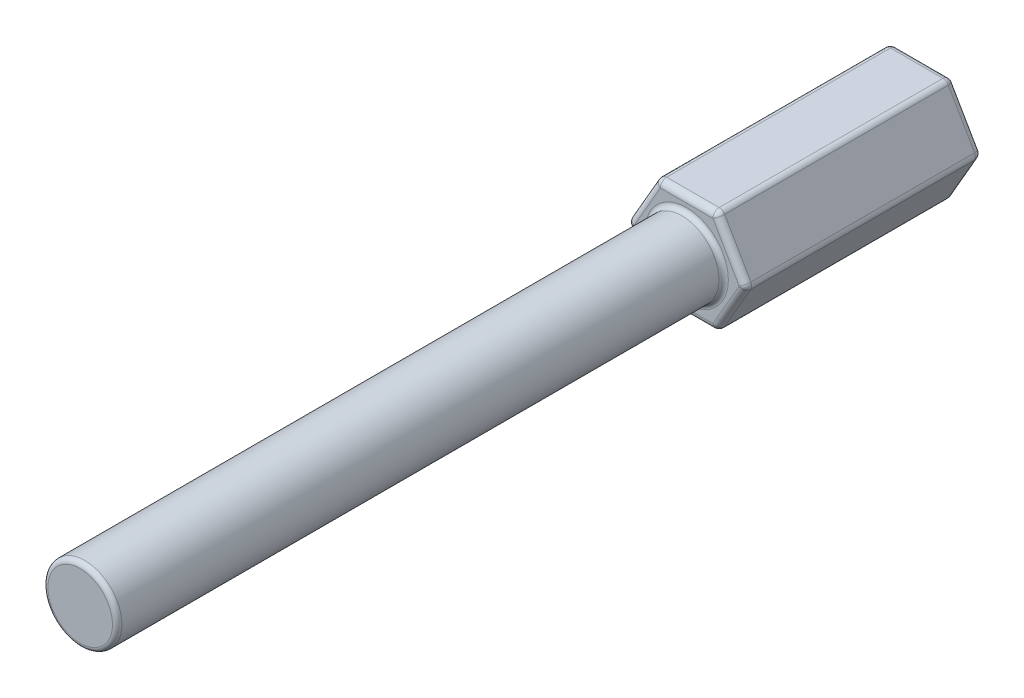
SolidWorks part; units mm, degrees
ref_plane "Front Plane" through (0, 0, 0) normal (0, 0, 1) x (1, 0, 0)
ref_plane "Top Plane" through (0, 0, 0) normal (0, 1, 0) x (1, 0, 0)
ref_plane "Right Plane" through (0, 0, 0) normal (1, 0, 0) x (0, 0, -1)
sketch "Sketch1" plane through (0, 0, 0) normal (0, 0, 1) x (1, 0, 0)
  line L1 (2.4105, -4.1751) -> (4.821, 0)
  line L2 (4.821, 0) -> (2.4105, 4.1751)
  line L3 (2.4105, 4.1751) -> (-2.4105, 4.1751)
  line L4 (-2.4105, 4.1751) -> (-4.821, 0)
  line L5 (-4.821, 0) -> (-2.4105, -4.1751)
  line L6 (-2.4105, -4.1751) -> (2.4105, -4.1751)
  circle A0 centre (0, 0) radius 4.1751 construction
  dimension "D1" = 8.3503
extrude "Boss-Extrude1" add sketch "Sketch1" along normal blind 19.05
sketch "Sketch2" plane through (0, 0, 19.05) normal (0, 0, 1) x (1, 0, 0)
  circle A0 centre (0, 0) radius 2.9845
  dimension "D1" = 5.969
extrude "Boss-Extrude2" add sketch "Sketch2" along normal blind 48.895 contours A0
fillet "Fillet1" radius 0.381 1 edges at (2.9845, 0, 67.945)
fillet "Fillet2" radius 0.381 1 edges at (2.9845, 0, 19.05)
fillet "Fillet3" radius 0.508 12 edges at (3.6158, -2.0876, 0) (3.6158, 2.0876, 0) (0, -4.1751, 0) (0, 4.1751, 0) (-3.6158, -2.0876, 0) (-3.6158, 2.0876, 0) (3.6158, 2.0876, 19.05) (0, -4.1751, 19.05) (3.6158, -2.0876, 19.05) (0, 4.1751, 19.05) (-3.6158, 2.0876, 19.05) (-3.6158, -2.0876, 19.05)
fillet "Fillet4" radius 0.508 18 edges at (2.3246, 4.0263, 18.9012) (2.3246, 4.0263, 0.1488) (4.6492, 0, 18.9012) (4.6492, 0, 0.1488) (2.3246, -4.0263, 18.9012) (2.3246, -4.0263, 0.1488) (-2.3246, -4.0263, 18.9012) (-2.3246, -4.0263, 0.1488) (-2.3246, 4.0263, 18.9012) (-2.3246, 4.0263, 0.1488) (-4.6492, 0, 18.9012) (-4.6492, 0, 0.1488) (2.4105, 4.1751, 9.525) (4.821, 0, 9.525) (2.4105, -4.1751, 9.525) (-2.4105, -4.1751, 9.525) (-2.4105, 4.1751, 9.525) (-4.821, 0, 9.525)
